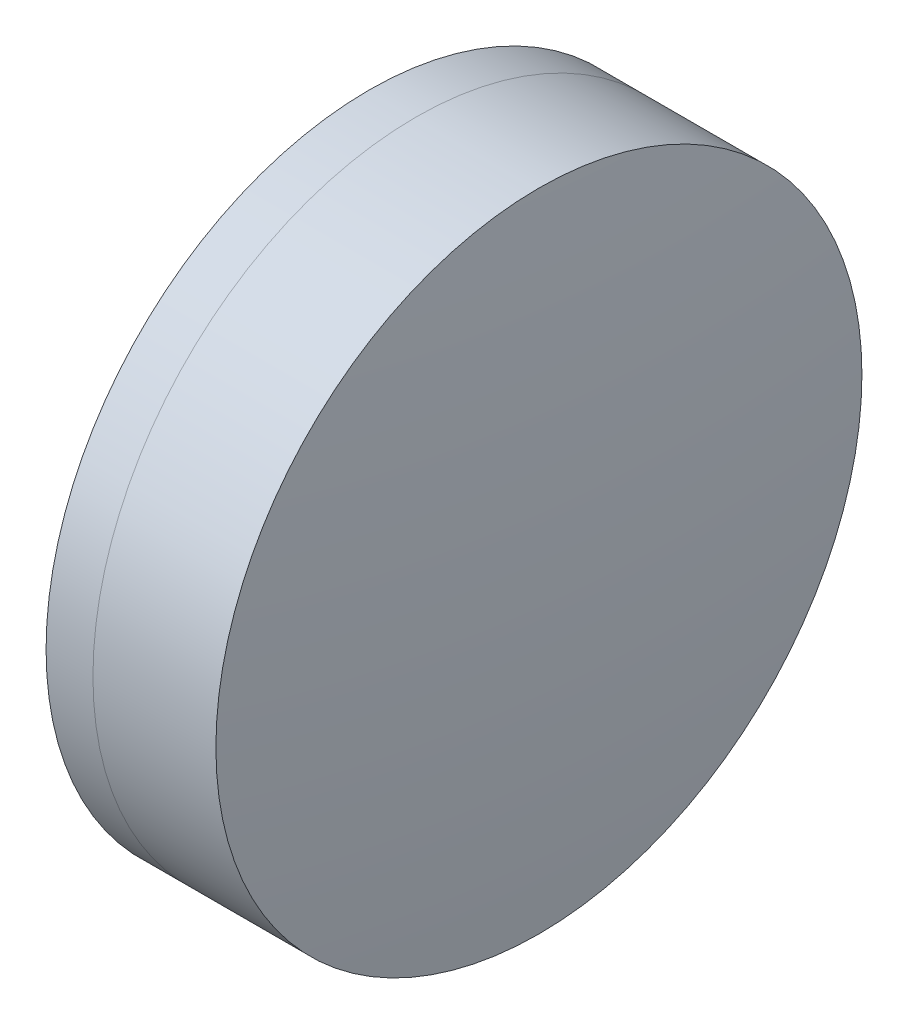
SolidWorks part; units mm, degrees
ref_plane "前视基准面" through (0, 0, 0) normal (0, 0, 1) x (1, 0, 0)
ref_plane "上视基准面" through (0, 0, 0) normal (0, 1, 0) x (1, 0, 0)
ref_plane "右视基准面" through (0, 0, 0) normal (1, 0, 0) x (0, 0, -1)
sketch "草图1" plane through (0, 0, 0) normal (0, 1, 0) x (1, 0, 0)
  line L0 (124.5233, 0) -> (395.1269, 0) construction
  line L1 (256.5849, -20) -> (259.4868, -20)
  line L2 (256.5849, 20) -> (259.4868, 20)
  arc A0 (259.4868, -20) -> (259.4868, 20) centre (230.0842, 0) ccw
  arc A1 (256.5849, 20) -> (256.5849, -20) centre (294.5942, 0) ccw
  point P10 (251.6442, 0)
  point P11 (265.6442, 0)
  dimension "D3" = 42.95
  dimension "D4" = 35.56
  dimension "D1" = 20
  dimension "D2" = 20
  dimension "D5" = 14
revolve "旋转1" add sketch "草图1" angle 360 about L0
sketch "草图2" plane through (0, 0, 0) normal (0, 1, 0) x (1, 0, 0)
  line L0 (-0.5519, 0) -> (409.4962, 0) construction
  line L2 (259.4868, 20) -> (267.0989, 20)
  line L3 (259.4868, -20) -> (267.0989, -20)
  arc A0 (267.0989, -20) -> (267.0989, 20) centre (76.2742, 0) ccw
  arc A1 (259.4868, -20) -> (259.4868, 20) centre (230.0842, 0) ccw construction
  arc A2 (259.4868, -20) -> (259.4868, 20) centre (230.0842, 0) ccw
  point P4 (265.6442, 0)
  point P8 (268.1442, 0)
  dimension "D1" = 191.87
  dimension "D2" = 2.5
revolve "旋转3" add sketch "草图2" angle 360 about L0
